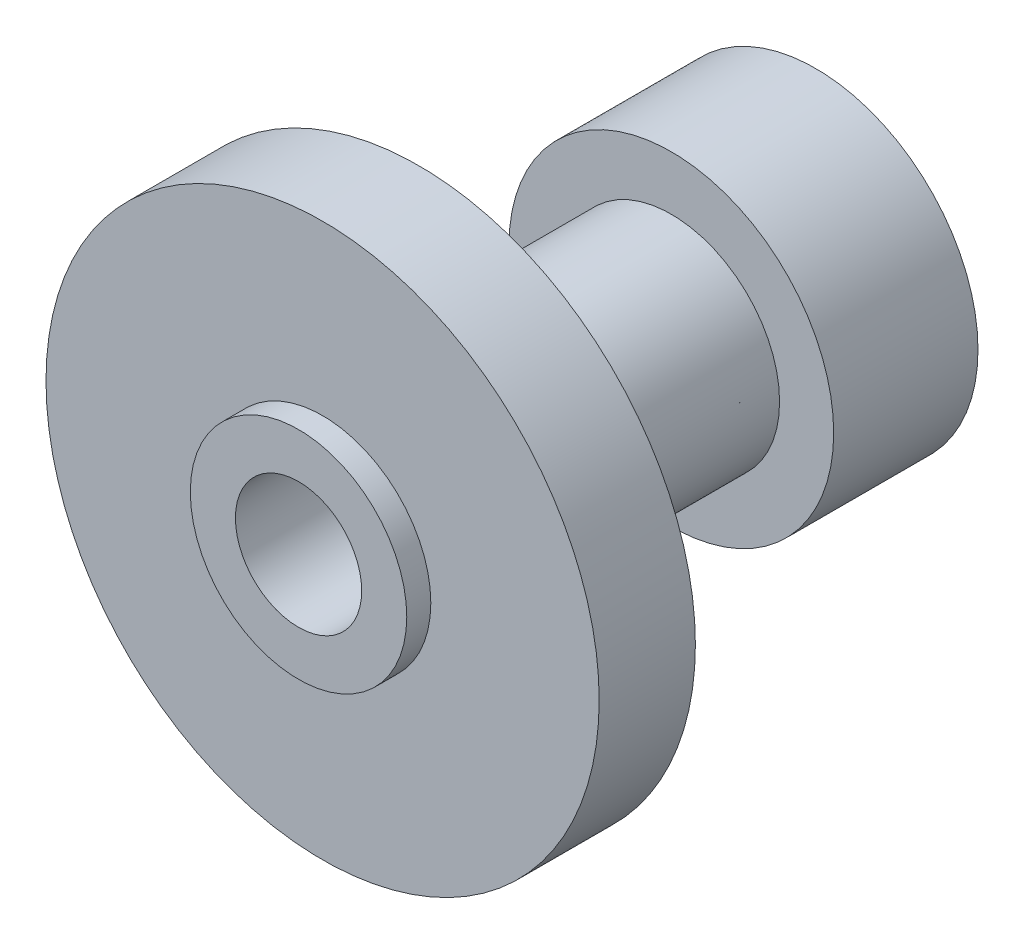
SolidWorks part; units mm, degrees
ref_plane "Front" through (0, 0, 0) normal (0, 0, 1) x (1, 0, 0)
ref_plane "Top" through (0, 0, 0) normal (0, 1, 0) x (1, 0, 0)
ref_plane "Right" through (0, 0, 0) normal (1, 0, 0) x (0, 0, -1)
other "Configuration Table"
sketch "Эскиз1" plane through (0, 0, 0) normal (0, 0, 1) x (1, 0, 0)
  circle A0 centre (0, 0) radius 23
extrude "Бобышка-Вытянуть1" add sketch "Эскиз1" along normal blind 8
sketch "Эскиз2" plane through (0, 0, 8) normal (0, 0, 1) x (1, 0, 0)
  circle A0 centre (0, 0) radius 9
extrude "Бобышка-Вытянуть2" add sketch "Эскиз2" along normal blind 2
sketch "Эскиз3" plane through (0, 0, 0) normal (0, 0, -1) x (-1, 0, 0)
  circle A0 centre (0, 0) radius 9
extrude "Бобышка-Вытянуть3" add sketch "Эскиз3" along normal blind 21
sketch "Эскиз4" plane through (0, 0, -21) normal (0, 0, -1) x (-1, 0, 0)
  circle A0 centre (0, 0) radius 13.5
extrude "Бобышка-Вытянуть4" add sketch "Эскиз4" along normal blind 12
sketch "Эскиз5" plane through (0, 0, -33) normal (0, 0, -1) x (-1, 0, 0)
  circle A0 centre (0, 0) radius 7.5
extrude "Вырез-Вытянуть1" cut sketch "Эскиз5" against normal blind 4
sketch "Эскиз6" plane through (0, 0, -29) normal (0, 0, -1) x (-1, 0, 0)
  circle A0 centre (0, 0) radius 5.25
extrude "Вырез-Вытянуть2" cut sketch "Эскиз6" against normal blind 100
